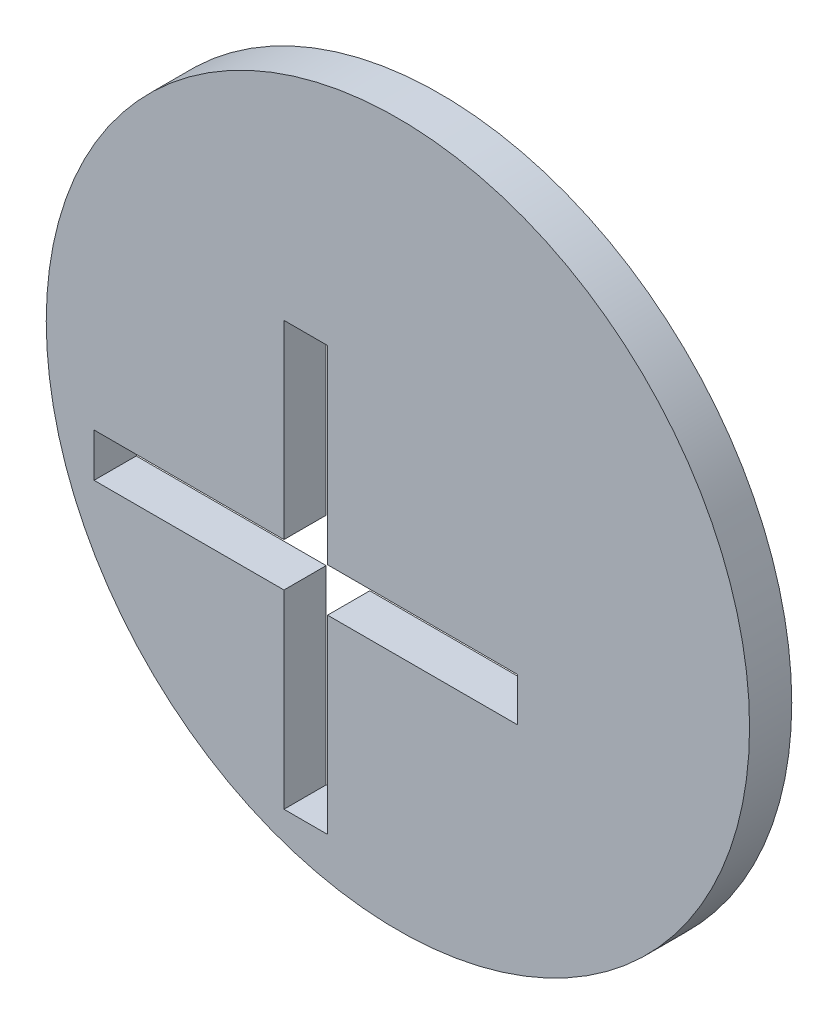
SolidWorks part; units mm, degrees
ref_plane "Front Plane" through (0, 0, 0) normal (0, 0, 1) x (1, 0, 0)
ref_plane "Top Plane" through (0, 0, 0) normal (0, 1, 0) x (1, 0, 0)
ref_plane "Right Plane" through (0, 0, 0) normal (1, 0, 0) x (0, 0, -1)
sketch "Sketch1" plane through (0, 0, 0) normal (0, 0, 1) x (1, 0, 0)
  line L0 (1.55, 1.55) -> (15.05, 1.55)
  line L1 (-15.05, 1.55) -> (-1.55, 1.55)
  line L2 (-15.05, 1.55) -> (-15.05, -1.55)
  line L3 (-15.05, -1.55) -> (-1.55, -1.55)
  line L4 (15.05, 1.55) -> (15.05, -1.55)
  line L5 (-15.05, 1.55) -> (15.05, -1.55) construction
  line L6 (-15.05, -1.55) -> (15.05, 1.55) construction
  line L7 (-1.55, -15.05) -> (1.55, -15.05)
  line L8 (-1.55, -15.05) -> (-1.55, -1.55)
  line L9 (-1.55, 15.05) -> (1.55, 15.05)
  line L10 (1.55, -15.05) -> (1.55, -1.55)
  line L11 (-1.55, -15.05) -> (1.55, 15.05) construction
  line L12 (-1.55, 15.05) -> (1.55, -15.05) construction
  line L13 (-1.55, 1.55) -> (-1.55, 15.05)
  line L14 (1.55, -1.55) -> (15.05, -1.55)
  line L15 (1.55, 1.55) -> (1.55, 15.05)
  circle A0 centre (6.55, 6.55) radius 25
  point P0 (0, 0)
  point P7 (0, 0)
  dimension "D6" = 50
  dimension "D1" = 3.1
  dimension "D2" = 3.1
  dimension "D3" = 30.1
  dimension "D4" = 30.1
  dimension "D5" = 5
  dimension "D7" = 5
extrude "Boss-Extrude1" add sketch "Sketch1" along normal mid plane 3
